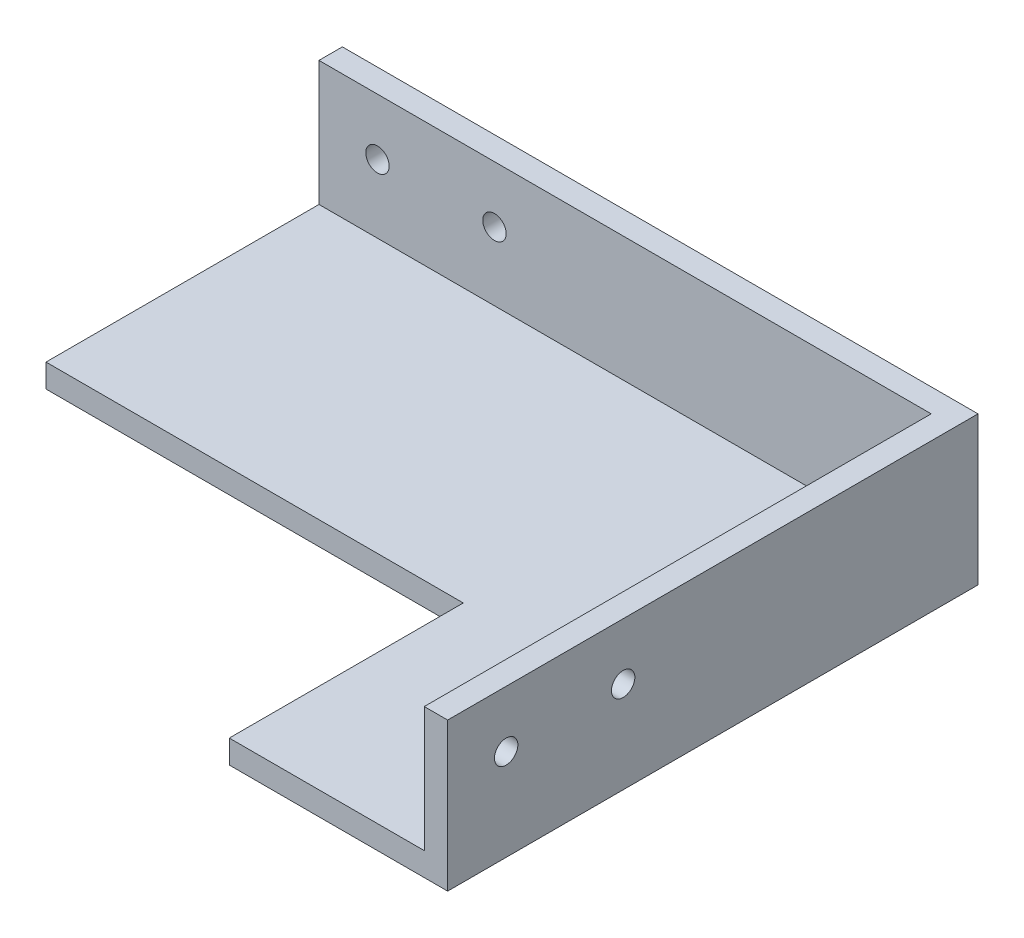
SolidWorks part; units mm, degrees
ref_plane "Alzado" through (0, 0, 0) normal (0, 0, 1) x (1, 0, 0)
ref_plane "Planta" through (0, 0, 0) normal (0, 1, 0) x (1, 0, 0)
ref_plane "Vista lateral" through (0, 0, 0) normal (1, 0, 0) x (0, 0, -1)
sketch "Croquis1" plane through (0, 0, 0) normal (0, 1, 0) x (1, 0, 0)
  line L0 (-39.25, -2.5) -> (14.25, -2.5)
  line L1 (-39.25, -32.5) -> (39.25, -32.5) construction
  line L2 (-39.25, -32.5) -> (-39.25, 32.5) construction
  line L3 (-39.25, 32.5) -> (39.25, 32.5) construction
  line L4 (39.25, -32.5) -> (39.25, 32.5) construction
  line L5 (-39.25, -32.5) -> (39.25, 32.5) construction
  line L6 (-39.25, 32.5) -> (39.25, -32.5) construction
  line L7 (14.25, -2.5) -> (14.25, -32.5)
  line L8 (14.25, -32.5) -> (39.25, -32.5)
  line L9 (39.25, -32.5) -> (39.25, 32.5)
  line L10 (39.25, 32.5) -> (-39.25, 32.5)
  line L11 (-39.25, 32.5) -> (-39.25, -2.5)
  point P0 (0, 0)
  dimension "D1" = 78.5
  dimension "D2" = 65
  dimension "D3" = 30
  dimension "D4" = 53.5
extrude "Saliente-Extruir1" add sketch "Croquis1" along normal blind 3
sketch "Croquis2" plane through (39.25, 0, 0) normal (1, 0, 0) x (0, 0, -1)
  line L0 (32.5, 3) -> (32.5, 0) construction
  line L1 (-32.5, 0) -> (32.5, 0)
  line L2 (-32.5, 0) -> (-32.5, 19)
  line L3 (-32.5, 19) -> (32.5, 19)
  line L4 (32.5, 0) -> (32.5, 19)
  line L5 (-32.5, 3) -> (32.5, 3) construction
  dimension "D1" = 16
extrude "Saliente-Extruir2" add sketch "Croquis2" along normal blind 3
sketch "Croquis3" plane through (0, 0, -32.5) normal (0, 0, -1) x (-1, 0, 0)
  line L1 (39.25, 0) -> (-42.25, 0)
  line L2 (39.25, 0) -> (39.25, 19)
  line L3 (39.25, 19) -> (-42.25, 19)
  line L4 (-42.25, 0) -> (-42.25, 19)
extrude "Saliente-Extruir3" add sketch "Croquis3" along normal blind 3
sketch "Croquis4" plane through (0, 0, -35.5) normal (0, 0, -1) x (-1, 0, 0)
  line L2 (39.25, 3) -> (-14.25, 3) construction
  line L4 (39.25, 0) -> (39.25, 19) construction
  circle A0 centre (31.75, 11.75) radius 1.5
  circle A1 centre (16.75, 11.75) radius 1.5
  dimension "D1" = 3
  dimension "D4" = 8.75
  dimension "D2" = 15
  dimension "D3" = 7.5
extrude "Cortar-Extruir1" cut sketch "Croquis4" against normal through all
sketch "Croquis5" plane through (42.25, 0, 0) normal (1, 0, 0) x (0, 0, -1)
  line L0 (-32.5, 19) -> (-32.5, 0) construction
  line L2 (-2.5, 3) -> (-32.5, 3) construction
  circle A0 centre (-25, 11.75) radius 1.5
  circle A1 centre (-10, 11.75) radius 1.5
  dimension "D2" = 3
  dimension "D3" = 7.5
  dimension "D4" = 8.75
  dimension "D1" = 15
extrude "Cortar-Extruir2" cut sketch "Croquis5" against normal through all
